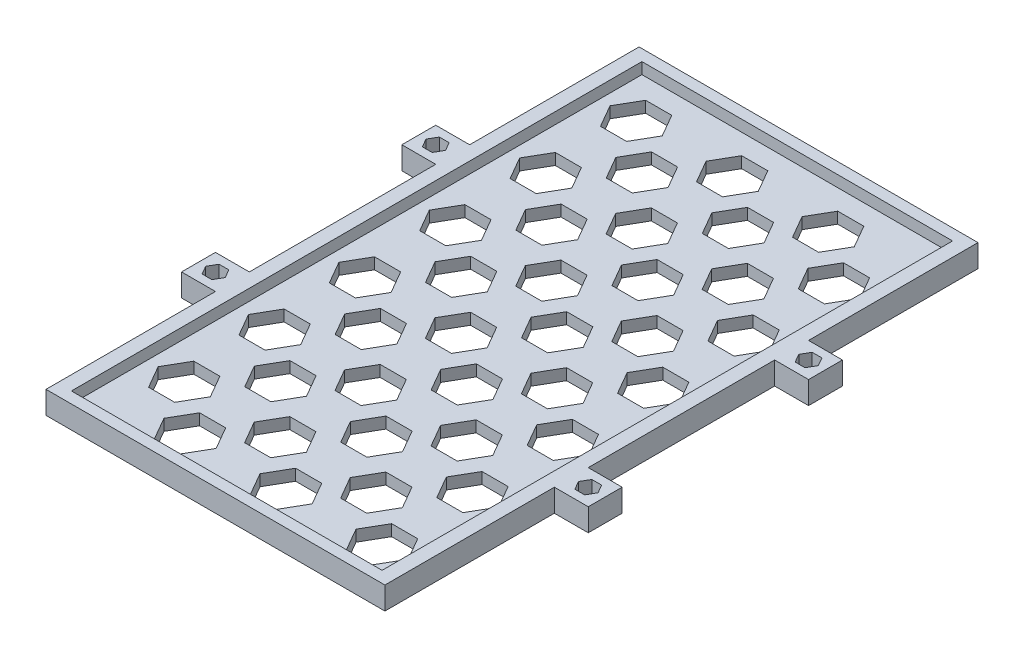
SolidWorks part; units mm, degrees
ref_plane "Alzado" through (0, 0, 0) normal (0, 0, 1) x (1, 0, 0)
ref_plane "Planta" through (0, 0, 0) normal (0, 1, 0) x (1, 0, 0)
ref_plane "Vista lateral" through (0, 0, 0) normal (1, 0, 0) x (0, 0, -1)
sketch "Croquis1" plane through (0, 0, 0) normal (0, 1, 0) x (1, 0, 0)
  line L0 (30, -52.5) -> (30, -22.5)
  line L1 (-30, 52.5) -> (30, 52.5)
  line L2 (30, -22.5) -> (30, -16.5) construction
  line L3 (-30, -52.5) -> (30, -52.5)
  line L4 (30, 16.5) -> (30, 22.5) construction
  line L5 (-30, 52.5) -> (30, -52.5) construction
  line L6 (-30, -52.5) -> (30, 52.5) construction
  line L7 (30, -22.5) -> (36, -22.5)
  line L8 (36, -22.5) -> (36, -16.5)
  line L9 (36, -16.5) -> (30, -16.5)
  line L10 (30, -16.5) -> (30, 16.5)
  line L11 (30, 16.5) -> (36, 16.5)
  line L12 (36, 16.5) -> (36, 22.5)
  line L13 (36, 22.5) -> (30, 22.5)
  line L14 (30, 22.5) -> (30, 52.5)
  line L15 (-30, 52.5) -> (-30, 22.5)
  line L16 (-30, 22.5) -> (-36, 22.5)
  line L17 (-36, 22.5) -> (-36, 16.5)
  line L18 (-36, 16.5) -> (-30, 16.5)
  line L19 (-30, 16.5) -> (-30, -16.5)
  line L20 (-30, -16.5) -> (-36, -16.5)
  line L21 (-36, -16.5) -> (-36, -22.5)
  line L22 (-36, -22.5) -> (-30, -22.5)
  line L23 (-30, -22.5) -> (-30, -52.5)
  line L24 (-30, 16.5) -> (-30, 22.5) construction
  line L25 (-30, -22.5) -> (-30, -16.5) construction
  line L26 (36, -19.5) -> (30, -19.5) construction
  line L27 (36, 19.5) -> (30, 19.5) construction
  line L28 (31.2679, -19.5) -> (32.134, -21)
  line L29 (32.134, -21) -> (33.866, -21)
  line L30 (33.866, -21) -> (34.7321, -19.5)
  line L31 (34.7321, -19.5) -> (33.866, -18)
  line L32 (33.866, -18) -> (32.134, -18)
  line L33 (32.134, -18) -> (31.2679, -19.5)
  line L34 (-30, 19.5) -> (-36, 19.5) construction
  line L35 (-30, -19.5) -> (-36, -19.5) construction
  line L37 (31.2679, 19.5) -> (32.134, 18)
  line L38 (32.134, 18) -> (33.866, 18)
  line L39 (33.866, 18) -> (34.7321, 19.5)
  line L40 (34.7321, 19.5) -> (33.866, 21)
  line L41 (33.866, 21) -> (32.134, 21)
  line L42 (32.134, 21) -> (31.2679, 19.5)
  line L43 (-34.7321, 19.5) -> (-33.866, 18)
  line L44 (-33.866, 18) -> (-32.134, 18)
  line L45 (-32.134, 18) -> (-31.2679, 19.5)
  line L46 (-31.2679, 19.5) -> (-32.134, 21)
  line L47 (-32.134, 21) -> (-33.866, 21)
  line L48 (-33.866, 21) -> (-34.7321, 19.5)
  line L49 (-34.7321, -19.5) -> (-33.866, -21)
  line L50 (-33.866, -21) -> (-32.134, -21)
  line L51 (-32.134, -21) -> (-31.2679, -19.5)
  line L52 (-31.2679, -19.5) -> (-32.134, -18)
  line L53 (-32.134, -18) -> (-33.866, -18)
  line L54 (-33.866, -18) -> (-34.7321, -19.5)
  circle A0 centre (33, -19.5) radius 1.5 construction
  circle A1 centre (33, 19.5) radius 1.5 construction
  circle A2 centre (-33, 19.5) radius 1.5 construction
  circle A3 centre (-33, -19.5) radius 1.5 construction
  point P0 (0, 0)
  dimension "D3" = 3
  dimension "D1" = 45
  dimension "D2" = 60
  dimension "D4" = 6
  dimension "D5" = 30
extrude "Saliente-Extruir1" add sketch "Croquis1" along normal blind 4
sketch "Croquis2" plane through (0, 4, 0) normal (0, 1, 0) x (1, 0, 0)
  line L0 (30, 52.5) -> (-30, 52.5) construction
  line L1 (-27.5, 50.5) -> (27.5, 50.5)
  line L2 (-27.5, 50.5) -> (-27.5, -50.5)
  line L3 (-27.5, -50.5) -> (27.5, -50.5)
  line L4 (27.5, 50.5) -> (27.5, -50.5)
  line L5 (-27.5, 50.5) -> (27.5, -50.5) construction
  line L6 (-27.5, -50.5) -> (27.5, 50.5) construction
  point P0 (0, 0)
  dimension "D1" = 2
  dimension "D2" = 55
extrude "Cortar-Extruir1" cut sketch "Croquis2" against normal blind 2
sketch "Croquis3" plane through (0, 2, 0) normal (0, 1, 0) x (1, 0, 0)
  line L0 (21.5, -50.5) -> (21.5, -44.5) construction
  line L1 (-27.5, -50.5) -> (27.5, -50.5) construction
  line L2 (21.5, -44.5) -> (27.5, -44.5) construction
  line L3 (27.5, -50.5) -> (27.5, 50.5) construction
  line L4 (-0.1188, -44.5) -> (2.1906, -48.5)
  line L5 (16.8812, -44.5) -> (19.1906, -48.5)
  line L6 (19.1906, -48.5) -> (23.8094, -48.5)
  line L7 (2.1906, -48.5) -> (6.8094, -48.5)
  line L8 (23.8094, -48.5) -> (26.1188, -44.5)
  line L9 (26.1188, -44.5) -> (23.8094, -40.5)
  line L10 (23.8094, -40.5) -> (19.1906, -40.5)
  line L11 (19.1906, -40.5) -> (16.8812, -44.5)
  line L12 (6.8094, -48.5) -> (9.1188, -44.5)
  line L13 (8.453, -37.0981) -> (10.7624, -41.0981)
  line L14 (10.7624, -41.0981) -> (15.3812, -41.0981)
  line L15 (15.3812, -41.0981) -> (17.6906, -37.0981)
  line L16 (17.6906, -37.0981) -> (15.3812, -33.0981)
  line L17 (15.3812, -33.0981) -> (10.7624, -33.0981)
  line L18 (9.1188, -44.5) -> (6.8094, -40.5)
  line L19 (10.7624, -33.0981) -> (8.453, -37.0981)
  line L20 (6.8094, -40.5) -> (2.1906, -40.5)
  line L21 (2.1906, -40.5) -> (-0.1188, -44.5)
  line L22 (-8.547, -37.0981) -> (-6.2376, -41.0981)
  line L23 (-6.2376, -41.0981) -> (-1.6188, -41.0981)
  line L24 (-1.6188, -41.0981) -> (0.6906, -37.0981)
  line L25 (0.6906, -37.0981) -> (-1.6188, -33.0981)
  line L26 (-1.6188, -33.0981) -> (-6.2376, -33.0981)
  line L27 (-6.2376, -33.0981) -> (-8.547, -37.0981)
  line L28 (-17.1188, -44.5) -> (-14.8094, -48.5)
  line L29 (-14.8094, -48.5) -> (-10.1906, -48.5)
  line L30 (-10.1906, -48.5) -> (-7.8812, -44.5)
  line L31 (-7.8812, -44.5) -> (-10.1906, -40.5)
  line L32 (-10.1906, -40.5) -> (-14.8094, -40.5)
  line L33 (-14.8094, -40.5) -> (-17.1188, -44.5)
  line L34 (-25.547, -37.0981) -> (-23.2376, -41.0981)
  line L35 (-23.2376, -41.0981) -> (-18.6188, -41.0981)
  line L36 (-18.6188, -41.0981) -> (-16.3094, -37.0981)
  line L37 (-16.3094, -37.0981) -> (-18.6188, -33.0981)
  line L38 (-18.6188, -33.0981) -> (-23.2376, -33.0981)
  line L39 (-23.2376, -33.0981) -> (-25.547, -37.0981)
  line L40 (-0.1188, -28.5) -> (2.1906, -32.5)
  line L41 (2.1906, -32.5) -> (6.8094, -32.5)
  line L42 (6.8094, -32.5) -> (9.1188, -28.5)
  line L43 (9.1188, -28.5) -> (6.8094, -24.5)
  line L44 (6.8094, -24.5) -> (2.1906, -24.5)
  line L45 (2.1906, -24.5) -> (-0.1188, -28.5)
  line L46 (-8.547, -21.0981) -> (-6.2376, -25.0981)
  line L47 (-6.2376, -25.0981) -> (-1.6188, -25.0981)
  line L48 (-1.6188, -25.0981) -> (0.6906, -21.0981)
  line L49 (0.6906, -21.0981) -> (-1.6188, -17.0981)
  line L50 (-1.6188, -17.0981) -> (-6.2376, -17.0981)
  line L51 (-6.2376, -17.0981) -> (-8.547, -21.0981)
  line L52 (-17.1188, -28.5) -> (-14.8094, -32.5)
  line L53 (-14.8094, -32.5) -> (-10.1906, -32.5)
  line L54 (-10.1906, -32.5) -> (-7.8812, -28.5)
  line L55 (-7.8812, -28.5) -> (-10.1906, -24.5)
  line L56 (-10.1906, -24.5) -> (-14.8094, -24.5)
  line L57 (-14.8094, -24.5) -> (-17.1188, -28.5)
  line L58 (-25.547, -21.0981) -> (-23.2376, -25.0981)
  line L59 (-23.2376, -25.0981) -> (-18.6188, -25.0981)
  line L60 (-18.6188, -25.0981) -> (-16.3094, -21.0981)
  line L61 (-16.3094, -21.0981) -> (-18.6188, -17.0981)
  line L62 (-18.6188, -17.0981) -> (-23.2376, -17.0981)
  line L63 (-23.2376, -17.0981) -> (-25.547, -21.0981)
  line L64 (-0.1188, -12.5) -> (2.1906, -16.5)
  line L65 (2.1906, -16.5) -> (6.8094, -16.5)
  line L66 (6.8094, -16.5) -> (9.1188, -12.5)
  line L67 (9.1188, -12.5) -> (6.8094, -8.5)
  line L68 (6.8094, -8.5) -> (2.1906, -8.5)
  line L69 (2.1906, -8.5) -> (-0.1188, -12.5)
  line L70 (-8.547, -5.0981) -> (-6.2376, -9.0981)
  line L71 (-6.2376, -9.0981) -> (-1.6188, -9.0981)
  line L72 (-1.6188, -9.0981) -> (0.6906, -5.0981)
  line L73 (0.6906, -5.0981) -> (-1.6188, -1.0981)
  line L74 (-1.6188, -1.0981) -> (-6.2376, -1.0981)
  line L75 (-6.2376, -1.0981) -> (-8.547, -5.0981)
  line L76 (-17.1188, -12.5) -> (-14.8094, -16.5)
  line L77 (-14.8094, -16.5) -> (-10.1906, -16.5)
  line L78 (-10.1906, -16.5) -> (-7.8812, -12.5)
  line L79 (-7.8812, -12.5) -> (-10.1906, -8.5)
  line L80 (-10.1906, -8.5) -> (-14.8094, -8.5)
  line L81 (-14.8094, -8.5) -> (-17.1188, -12.5)
  line L82 (-25.547, -5.0981) -> (-23.2376, -9.0981)
  line L83 (-23.2376, -9.0981) -> (-18.6188, -9.0981)
  line L84 (-18.6188, -9.0981) -> (-16.3094, -5.0981)
  line L85 (-16.3094, -5.0981) -> (-18.6188, -1.0981)
  line L86 (-18.6188, -1.0981) -> (-23.2376, -1.0981)
  line L87 (-23.2376, -1.0981) -> (-25.547, -5.0981)
  line L88 (-0.1188, 3.5) -> (2.1906, -0.5)
  line L89 (2.1906, -0.5) -> (6.8094, -0.5)
  line L90 (6.8094, -0.5) -> (9.1188, 3.5)
  line L91 (9.1188, 3.5) -> (6.8094, 7.5)
  line L92 (6.8094, 7.5) -> (2.1906, 7.5)
  line L93 (2.1906, 7.5) -> (-0.1188, 3.5)
  line L94 (-8.547, 10.9019) -> (-6.2376, 6.9019)
  line L95 (-6.2376, 6.9019) -> (-1.6188, 6.9019)
  line L96 (-1.6188, 6.9019) -> (0.6906, 10.9019)
  line L97 (0.6906, 10.9019) -> (-1.6188, 14.9019)
  line L98 (-1.6188, 14.9019) -> (-6.2376, 14.9019)
  line L99 (-6.2376, 14.9019) -> (-8.547, 10.9019)
  line L100 (-17.1188, 3.5) -> (-14.8094, -0.5)
  line L101 (-14.8094, -0.5) -> (-10.1906, -0.5)
  line L102 (-10.1906, -0.5) -> (-7.8812, 3.5)
  line L103 (-7.8812, 3.5) -> (-10.1906, 7.5)
  line L104 (-10.1906, 7.5) -> (-14.8094, 7.5)
  line L105 (-14.8094, 7.5) -> (-17.1188, 3.5)
  line L106 (-25.547, 10.9019) -> (-23.2376, 6.9019)
  line L107 (-23.2376, 6.9019) -> (-18.6188, 6.9019)
  line L108 (-18.6188, 6.9019) -> (-16.3094, 10.9019)
  line L109 (-16.3094, 10.9019) -> (-18.6188, 14.9019)
  line L110 (-18.6188, 14.9019) -> (-23.2376, 14.9019)
  line L111 (-23.2376, 14.9019) -> (-25.547, 10.9019)
  line L112 (-0.1188, 19.5) -> (2.1906, 15.5)
  line L113 (2.1906, 15.5) -> (6.8094, 15.5)
  line L114 (6.8094, 15.5) -> (9.1188, 19.5)
  line L115 (9.1188, 19.5) -> (6.8094, 23.5)
  line L116 (6.8094, 23.5) -> (2.1906, 23.5)
  line L117 (2.1906, 23.5) -> (-0.1188, 19.5)
  line L118 (-8.547, 26.9019) -> (-6.2376, 22.9019)
  line L119 (-6.2376, 22.9019) -> (-1.6188, 22.9019)
  line L120 (-1.6188, 22.9019) -> (0.6906, 26.9019)
  line L121 (0.6906, 26.9019) -> (-1.6188, 30.9019)
  line L122 (-1.6188, 30.9019) -> (-6.2376, 30.9019)
  line L123 (-6.2376, 30.9019) -> (-8.547, 26.9019)
  line L124 (-17.1188, 19.5) -> (-14.8094, 15.5)
  line L125 (-14.8094, 15.5) -> (-10.1906, 15.5)
  line L126 (-10.1906, 15.5) -> (-7.8812, 19.5)
  line L127 (-7.8812, 19.5) -> (-10.1906, 23.5)
  line L128 (-10.1906, 23.5) -> (-14.8094, 23.5)
  line L129 (-14.8094, 23.5) -> (-17.1188, 19.5)
  line L130 (-25.547, 26.9019) -> (-23.2376, 22.9019)
  line L131 (-23.2376, 22.9019) -> (-18.6188, 22.9019)
  line L132 (-18.6188, 22.9019) -> (-16.3094, 26.9019)
  line L133 (-16.3094, 26.9019) -> (-18.6188, 30.9019)
  line L134 (-18.6188, 30.9019) -> (-23.2376, 30.9019)
  line L135 (-23.2376, 30.9019) -> (-25.547, 26.9019)
  line L136 (-0.1188, 35.5) -> (2.1906, 31.5)
  line L137 (2.1906, 31.5) -> (6.8094, 31.5)
  line L138 (6.8094, 31.5) -> (9.1188, 35.5)
  line L139 (9.1188, 35.5) -> (6.8094, 39.5)
  line L140 (6.8094, 39.5) -> (2.1906, 39.5)
  line L141 (2.1906, 39.5) -> (-0.1188, 35.5)
  line L142 (-8.547, 42.9019) -> (-6.2376, 38.9019)
  line L143 (-6.2376, 38.9019) -> (-1.6188, 38.9019)
  line L144 (-1.6188, 38.9019) -> (0.6906, 42.9019)
  line L145 (0.6906, 42.9019) -> (-1.6188, 46.9019)
  line L146 (-1.6188, 46.9019) -> (-6.2376, 46.9019)
  line L147 (-6.2376, 46.9019) -> (-8.547, 42.9019)
  line L148 (-17.1188, 35.5) -> (-14.8094, 31.5)
  line L149 (-14.8094, 31.5) -> (-10.1906, 31.5)
  line L150 (-10.1906, 31.5) -> (-7.8812, 35.5)
  line L151 (-7.8812, 35.5) -> (-10.1906, 39.5)
  line L152 (-10.1906, 39.5) -> (-14.8094, 39.5)
  line L153 (-14.8094, 39.5) -> (-17.1188, 35.5)
  line L154 (-25.547, 42.9019) -> (-23.2376, 38.9019)
  line L155 (-23.2376, 38.9019) -> (-18.6188, 38.9019)
  line L156 (-18.6188, 38.9019) -> (-16.3094, 42.9019)
  line L157 (-16.3094, 42.9019) -> (-18.6188, 46.9019)
  line L158 (-18.6188, 46.9019) -> (-23.2376, 46.9019)
  line L159 (-23.2376, 46.9019) -> (-25.547, 42.9019)
  line L160 (16.8812, -28.5) -> (19.1906, -32.5)
  line L161 (19.1906, -32.5) -> (23.8094, -32.5)
  line L162 (23.8094, -32.5) -> (26.1188, -28.5)
  line L163 (26.1188, -28.5) -> (23.8094, -24.5)
  line L164 (23.8094, -24.5) -> (19.1906, -24.5)
  line L165 (19.1906, -24.5) -> (16.8812, -28.5)
  line L166 (8.453, -21.0981) -> (10.7624, -25.0981)
  line L167 (10.7624, -25.0981) -> (15.3812, -25.0981)
  line L168 (15.3812, -25.0981) -> (17.6906, -21.0981)
  line L169 (17.6906, -21.0981) -> (15.3812, -17.0981)
  line L170 (15.3812, -17.0981) -> (10.7624, -17.0981)
  line L171 (10.7624, -17.0981) -> (8.453, -21.0981)
  line L172 (16.8812, -12.5) -> (19.1906, -16.5)
  line L173 (19.1906, -16.5) -> (23.8094, -16.5)
  line L174 (23.8094, -16.5) -> (26.1188, -12.5)
  line L175 (26.1188, -12.5) -> (23.8094, -8.5)
  line L176 (23.8094, -8.5) -> (19.1906, -8.5)
  line L177 (19.1906, -8.5) -> (16.8812, -12.5)
  line L178 (8.453, -5.0981) -> (10.7624, -9.0981)
  line L179 (10.7624, -9.0981) -> (15.3812, -9.0981)
  line L180 (15.3812, -9.0981) -> (17.6906, -5.0981)
  line L181 (17.6906, -5.0981) -> (15.3812, -1.0981)
  line L182 (15.3812, -1.0981) -> (10.7624, -1.0981)
  line L183 (10.7624, -1.0981) -> (8.453, -5.0981)
  line L184 (16.8812, 3.5) -> (19.1906, -0.5)
  line L185 (19.1906, -0.5) -> (23.8094, -0.5)
  line L186 (23.8094, -0.5) -> (26.1188, 3.5)
  line L187 (26.1188, 3.5) -> (23.8094, 7.5)
  line L188 (23.8094, 7.5) -> (19.1906, 7.5)
  line L189 (19.1906, 7.5) -> (16.8812, 3.5)
  line L190 (8.453, 10.9019) -> (10.7624, 6.9019)
  line L191 (10.7624, 6.9019) -> (15.3812, 6.9019)
  line L192 (15.3812, 6.9019) -> (17.6906, 10.9019)
  line L193 (17.6906, 10.9019) -> (15.3812, 14.9019)
  line L194 (15.3812, 14.9019) -> (10.7624, 14.9019)
  line L195 (10.7624, 14.9019) -> (8.453, 10.9019)
  line L196 (16.8812, 19.5) -> (19.1906, 15.5)
  line L197 (19.1906, 15.5) -> (23.8094, 15.5)
  line L198 (23.8094, 15.5) -> (26.1188, 19.5)
  line L199 (26.1188, 19.5) -> (23.8094, 23.5)
  line L200 (23.8094, 23.5) -> (19.1906, 23.5)
  line L201 (19.1906, 23.5) -> (16.8812, 19.5)
  line L202 (8.453, 26.9019) -> (10.7624, 22.9019)
  line L203 (10.7624, 22.9019) -> (15.3812, 22.9019)
  line L204 (15.3812, 22.9019) -> (17.6906, 26.9019)
  line L205 (17.6906, 26.9019) -> (15.3812, 30.9019)
  line L206 (15.3812, 30.9019) -> (10.7624, 30.9019)
  line L207 (10.7624, 30.9019) -> (8.453, 26.9019)
  line L208 (16.8812, 35.5) -> (19.1906, 31.5)
  line L209 (19.1906, 31.5) -> (23.8094, 31.5)
  line L210 (23.8094, 31.5) -> (26.1188, 35.5)
  line L211 (26.1188, 35.5) -> (23.8094, 39.5)
  line L212 (23.8094, 39.5) -> (19.1906, 39.5)
  line L213 (19.1906, 39.5) -> (16.8812, 35.5)
  line L214 (8.453, 42.9019) -> (10.7624, 38.9019)
  line L215 (10.7624, 38.9019) -> (15.3812, 38.9019)
  line L216 (15.3812, 38.9019) -> (17.6906, 42.9019)
  line L217 (17.6906, 42.9019) -> (15.3812, 46.9019)
  line L218 (15.3812, 46.9019) -> (10.7624, 46.9019)
  line L219 (10.7624, 46.9019) -> (8.453, 42.9019)
  circle A0 centre (21.5, -44.5) radius 4 construction
  circle A1 centre (13.0718, -37.0981) radius 4 construction
  circle A2 centre (4.5, -44.5) radius 4 construction
  circle A3 centre (-3.9282, -37.0981) radius 4 construction
  circle A4 centre (-12.5, -44.5) radius 4 construction
  circle A5 centre (-20.9282, -37.0981) radius 4 construction
  circle A6 centre (4.5, -28.5) radius 4 construction
  circle A7 centre (-3.9282, -21.0981) radius 4 construction
  circle A8 centre (-12.5, -28.5) radius 4 construction
  circle A9 centre (-20.9282, -21.0981) radius 4 construction
  circle A10 centre (4.5, -12.5) radius 4 construction
  circle A11 centre (-3.9282, -5.0981) radius 4 construction
  circle A12 centre (-12.5, -12.5) radius 4 construction
  circle A13 centre (-20.9282, -5.0981) radius 4 construction
  circle A14 centre (4.5, 3.5) radius 4 construction
  circle A15 centre (-3.9282, 10.9019) radius 4 construction
  circle A16 centre (-12.5, 3.5) radius 4 construction
  circle A17 centre (-20.9282, 10.9019) radius 4 construction
  circle A18 centre (4.5, 19.5) radius 4 construction
  circle A19 centre (-3.9282, 26.9019) radius 4 construction
  circle A20 centre (-12.5, 19.5) radius 4 construction
  circle A21 centre (-20.9282, 26.9019) radius 4 construction
  circle A22 centre (4.5, 35.5) radius 4 construction
  circle A23 centre (-3.9282, 42.9019) radius 4 construction
  circle A24 centre (-12.5, 35.5) radius 4 construction
  circle A25 centre (-20.9282, 42.9019) radius 4 construction
  circle A26 centre (21.5, -28.5) radius 4 construction
  circle A27 centre (13.0718, -21.0981) radius 4 construction
  circle A28 centre (21.5, -12.5) radius 4 construction
  circle A29 centre (13.0718, -5.0981) radius 4 construction
  circle A30 centre (21.5, 3.5) radius 4 construction
  circle A31 centre (13.0718, 10.9019) radius 4 construction
  circle A32 centre (21.5, 19.5) radius 4 construction
  circle A33 centre (13.0718, 26.9019) radius 4 construction
  circle A34 centre (21.5, 35.5) radius 4 construction
  circle A35 centre (13.0718, 42.9019) radius 4 construction
  dimension "D1" = 3
  dimension "D3" = 8
  dimension "D2" = 6
  dimension "D4" = 1.5
  dimension "D5" = 3
  dimension "D6" = 6
extrude "Cortar-Extruir2" cut sketch "Croquis3" against normal through all
